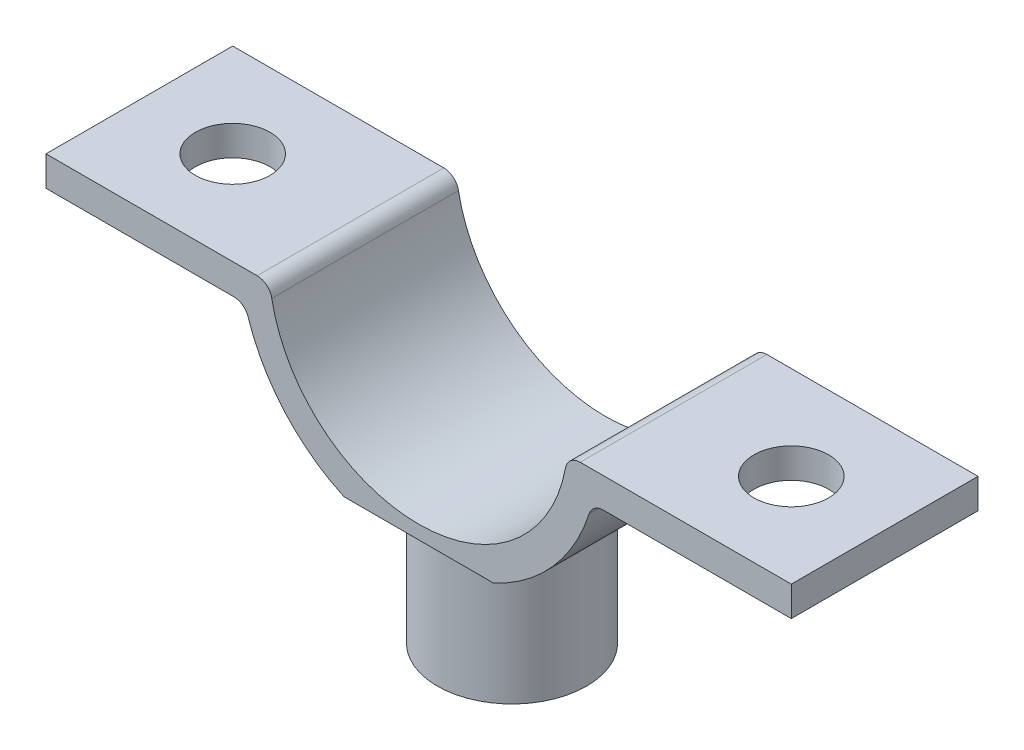
SolidWorks part; units mm, degrees
ref_plane "Front Plane" through (0, 0, 0) normal (0, 0, 1) x (1, 0, 0)
ref_plane "Top Plane" through (0, 0, 0) normal (0, 1, 0) x (1, 0, 0)
ref_plane "Right Plane" through (0, 0, 0) normal (1, 0, 0) x (0, 0, -1)
sketch "Sketch1" plane through (0, 0, 0) normal (0, 0, 1) x (1, 0, 0)
  line L0 (0, 0) -> (0, 50000) construction
  line L1 (0, 0) -> (50000, 0) construction
  line L2 (0, 0) -> (0, 20.0173) construction
  line L15 (0, 20.0173) -> (0, 19.0173) construction
  line L16 (-10.8167, 19.0173) -> (-19.9499, 19.0173)
  line L18 (-19.9499, 17.0173) -> (-12.3693, 17.0173)
  line L19 (10.8167, 19.0173) -> (19.9499, 19.0173)
  line L21 (19.9499, 17.0173) -> (12.3693, 17.0173)
  line L22 (-19.9499, 19.0173) -> (-24.9499, 19.0173)
  line L23 (5, 9.1086) -> (5, 0)
  line L24 (5, 0) -> (-5, 0)
  line L25 (-5, 0) -> (-5, 9.1086)
  line L26 (-24.9499, 19.0173) -> (-24.9499, 17.0173)
  line L27 (-24.9499, 17.0173) -> (-19.9499, 17.0173)
  line L28 (19.9499, 19.0173) -> (24.9499, 19.0173)
  line L29 (24.9499, 19.0173) -> (24.9499, 17.0173)
  line L30 (24.9499, 17.0173) -> (19.9499, 17.0173)
  arc A0 (-9.8333, 18.1991) -> (9.8333, 18.1991) centre (0, 20.0173) ccw
  arc A3 (-11.4178, 16.325) -> (-5, 9.1086) centre (0, 20.0173) ccw
  arc A4 (12.3693, 17.0173) -> (11.4178, 16.325) centre (12.3693, 16.0173) ccw
  arc A5 (10.8167, 19.0173) -> (9.8333, 18.1991) centre (10.8167, 18.0173) ccw
  arc A6 (-12.3693, 17.0173) -> (-11.4178, 16.325) centre (-12.3693, 16.0173) cw
  arc A7 (-10.8167, 19.0173) -> (-9.8333, 18.1991) centre (-10.8167, 18.0173) cw
  arc A8 (5, 9.1086) -> (11.4178, 16.325) centre (0, 20.0173) ccw
  point P18 (11.619, 17.0173)
  point P21 (9.9499, 19.0173)
  point P24 (-11.619, 17.0173)
  point P27 (-9.9499, 19.0173)
  dimension "D1" = 1
extrude "Boss-Extrude1" add sketch "Sketch1" along normal blind 12.5
sketch "Sketch4" plane through (0, 0, 0) normal (0, -1, 0) x (1, 0, 0)
  line L0 (0, 0) -> (0, 12.5) construction
  line L1 (-5, 12.5) -> (5, 12.5) construction
  circle A0 centre (0, 6.25) radius 5
extrude "Cut-Extrude6" cut sketch "Sketch4" against normal blind 9.11 flip side to cut
sketch "Sketch5" plane through (0, 0, 0) normal (0, -1, 0) x (1, 0, 0)
  circle A0 centre (0, 6.25) radius 3
extrude "Cut-Extrude7" cut sketch "Sketch5" against normal blind 9.11
sketch "Sketch6" plane through (0, 19.0173, 0) normal (0, 1, 0) x (1, 0, 0)
  line L0 (-24.9499, -6.25) -> (-18.6999, -6.25) construction
  line L1 (-24.9499, -12.5) -> (-24.9499, 0) construction
  line L2 (0, 0) -> (0, -12.5) construction
  line L3 (-9.8333, -12.5) -> (9.8333, -12.5) construction
  circle A0 centre (-18.6999, -6.25) radius 2.5
  circle A1 centre (18.6999, -6.25) radius 2.5
extrude "Cut-Extrude8" cut sketch "Sketch6" against normal up to next
